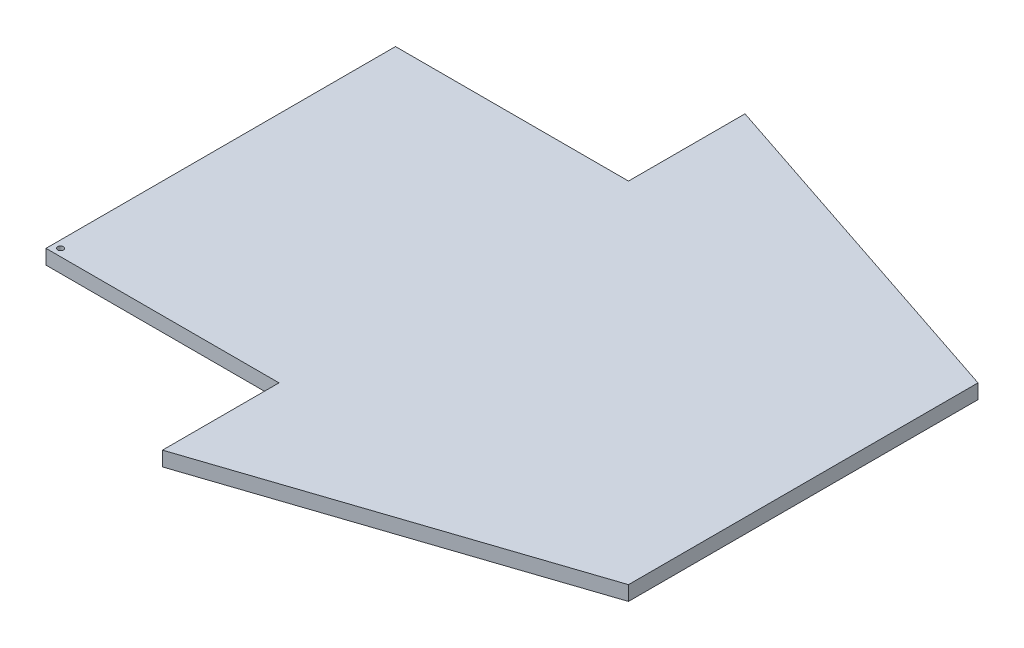
SolidWorks part; units mm, degrees
material "Balsa"
ref_plane "Front Plane" through (0, 0, 0) normal (0, 0, 1) x (1, 0, 0)
ref_plane "Top Plane" through (0, 0, 0) normal (0, 1, 0) x (1, 0, 0)
ref_plane "Right Plane" through (0, 0, 0) normal (1, 0, 0) x (0, 0, -1)
sketch "Sketch1" plane through (0, 0, 0) normal (0, 1, 0) x (1, 0, 0)
  line L1 (0, 254) -> (152.4, 203.2)
  line L2 (152.4, 203.2) -> (152.4, 50.8)
  line L3 (152.4, 50.8) -> (0, 0)
  line L4 (0, 0) -> (0, 50.8)
  line L5 (0, 50.8) -> (-101.6, 50.8)
  line L6 (-101.6, 50.8) -> (-101.6, 203.2)
  line L7 (-101.6, 203.2) -> (0, 203.2)
  line L8 (0, 203.2) -> (0, 254)
  dimension "D1" = 254
  dimension "D2" = 152.4
  dimension "D3" = 152.4
  dimension "D4" = 50.8
  dimension "D5" = 101.6
extrude "Main fin" add sketch "Sketch1" along normal blind 6.35
sketch "Sketch2" plane through (0, 0, 0) normal (0, -1, 0) x (-1, 0, 0)
  line L0 (101.6, 203.2) -> (101.6, 50.8) construction
  line L2 (101.6, 50.8) -> (0, 50.8) construction
  circle A0 centre (98.425, 53.975) radius 1.27
  dimension "D1" = 2.54
  dimension "D2" = 3.175
  dimension "D3" = 3.175
extrude "Pin hole" cut sketch "Sketch2" against normal through all
equation "\"1o\"=3.16863"
